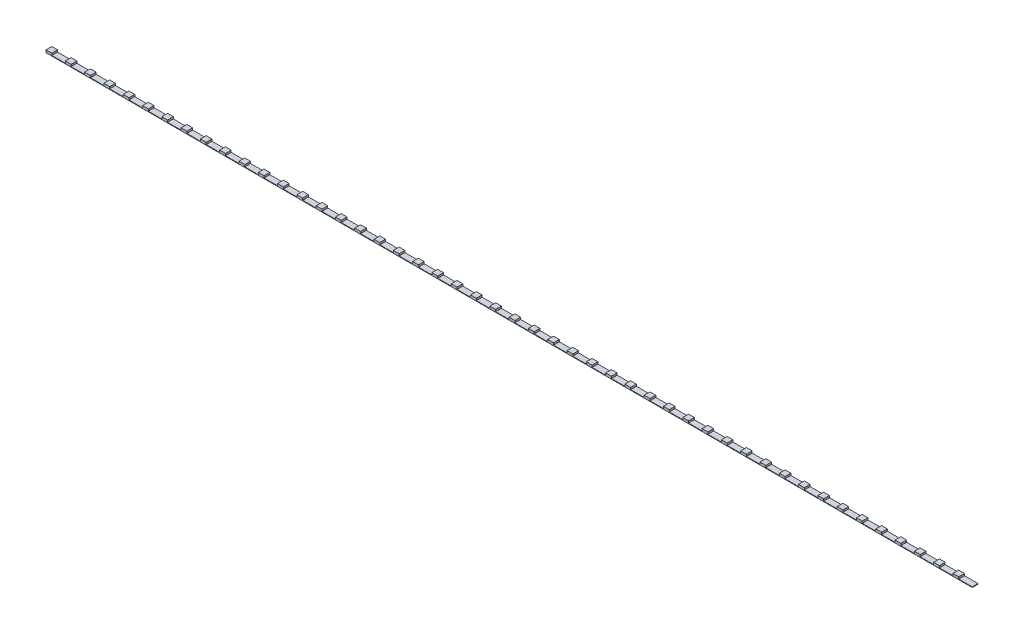
SolidWorks part; units mm, degrees
material "6061-T6 (SS)"
ref_plane "前视基准面" through (0, 0, 0) normal (0, 0, 1) x (1, 0, 0)
ref_plane "上视基准面" through (0, 0, 0) normal (0, 1, 0) x (1, 0, 0)
ref_plane "右视基准面" through (0, 0, 0) normal (1, 0, 0) x (0, 0, -1)
sketch "草图1" plane through (0, 0, 0) normal (0, 1, 0) x (1, 0, 0)
  line L1 (-400, 2.5) -> (400, 2.5)
  line L2 (-400, 2.5) -> (-400, -2.5)
  line L3 (-400, -2.5) -> (400, -2.5)
  line L4 (400, 2.5) -> (400, -2.5)
  line L5 (-400, 2.5) -> (400, -2.5) construction
  line L6 (-400, -2.5) -> (400, 2.5) construction
  point P0 (0, 0)
  dimension "D1" = 5
  dimension "D2" = 800
extrude "凸台-拉伸1" add sketch "草图1" along normal blind 0.5
sketch "草图2" plane through (0, 0.5, 0) normal (0, 1, 0) x (1, 0, 0)
  line L0 (400, 2.5) -> (-400, 2.5) construction
  line L1 (-400, -2.5) -> (-395, -2.5)
  line L2 (-400, -2.5) -> (-400, 2.5)
  line L3 (-400, 2.5) -> (-395, 2.5)
  line L4 (-395, -2.5) -> (-395, 2.5)
  dimension "D1" = 5
extrude "凸台-拉伸2" add sketch "草图2" along normal blind 1.7
pattern_linear "阵列(线性)1" count 48 spacing 16.6667 along (1, 0, 0) of "凸台-拉伸2"
